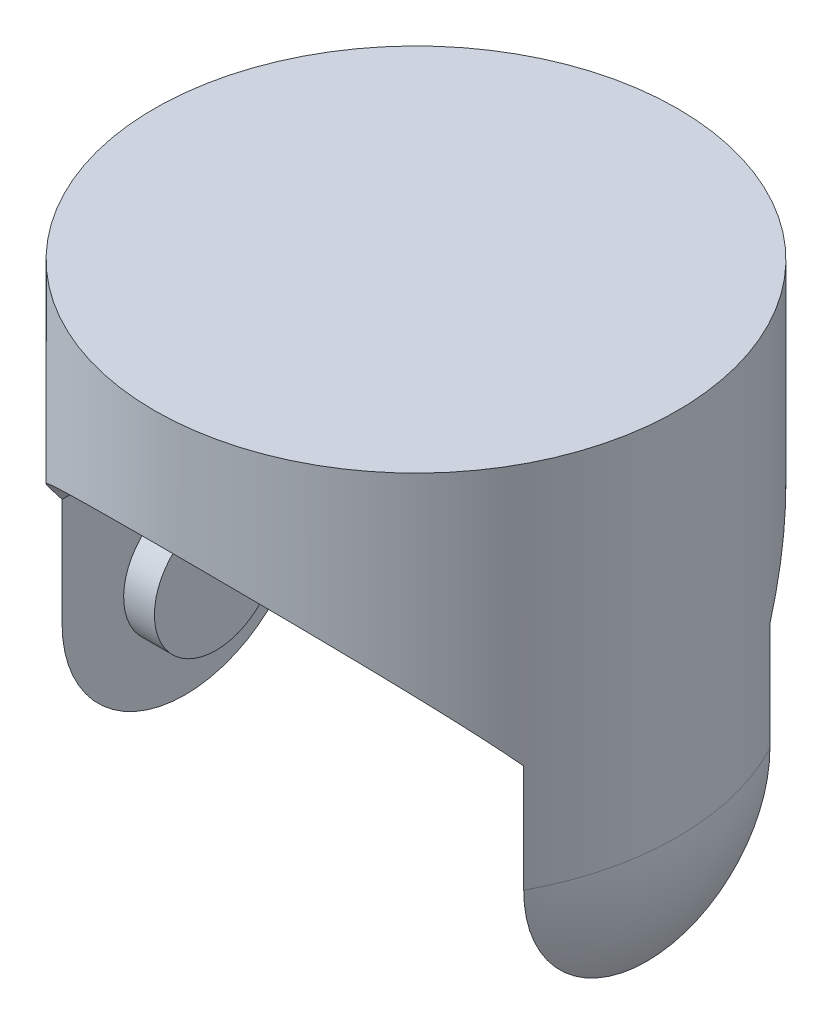
SolidWorks part; units mm, degrees
ref_plane "Front Plane" through (0, 0, 0) normal (0, 0, 1) x (1, 0, 0)
ref_plane "Top Plane" through (0, 0, 0) normal (0, 1, 0) x (1, 0, 0)
ref_plane "Right Plane" through (0, 0, 0) normal (1, 0, 0) x (0, 0, -1)
sketch "Sketch2" plane through (0, 0, 0) normal (0, 0, 1) x (1, 0, 0)
  line L0 (0, 0) -> (215.9, 0)
  line L1 (215.9, 0) -> (215.9, -304.8)
  line L2 (0, 0) -> (0, -648.3311) construction
  line L3 (0, 0) -> (0, -520.7)
  arc A0 (215.9, -304.8) -> (0, -520.7) centre (0, -304.8) cw
  dimension "D1" = 215.9
  dimension "D2" = 304.8
revolve "Revolve1" add sketch "Sketch2" angle 360 about L2
sketch "Sketch3" plane through (0, 0, 0) normal (0, 0, 1) x (1, 0, 0)
  line L0 (0, 0) -> (0, -520.7) construction
  line L1 (190.5, -215.9) -> (190.5, -546.1)
  line L2 (190.5, -546.1) -> (-190.5, -546.1)
  line L3 (215.9, -304.8) -> (215.9, 0) construction
  line L4 (215.9, -304.8) -> (-215.9, -304.8) construction
  line L5 (-190.5, -215.9) -> (-190.5, -546.1)
  arc A0 (-215.9, -304.8) -> (215.9, -304.8) centre (0, -304.8) ccw construction
  arc A1 (190.5, -215.9) -> (-190.5, -215.9) centre (0, -304.8) ccw
  point P16 (0, -546.1)
  dimension "D1" = 25.4
  dimension "D2" = 25.4
  dimension "D3" = 330.2
extrude "Cut-Extrude1" cut sketch "Sketch3" against normal through all both and the other way through all
sketch "Sketch4" plane through (-190.5, 0, 0) normal (1, 0, 0) x (0, 0, -1)
  line L0 (0, -215.9) -> (0, -406.4) construction
  line L1 (101.6, -215.9) -> (-101.6, -215.9) construction
  arc A0 (-101.6, -304.8) -> (101.6, -304.8) centre (0, -304.8) ccw construction
  circle A1 centre (0, -311.15) radius 50.8
  dimension "D1" = 101.6
extrude "Boss-Extrude1" add sketch "Sketch4" along normal blind 25.4
mirror "Mirror1" about plane through (0, 0, 0) normal (1, 0, 0) of "Boss-Extrude1"
